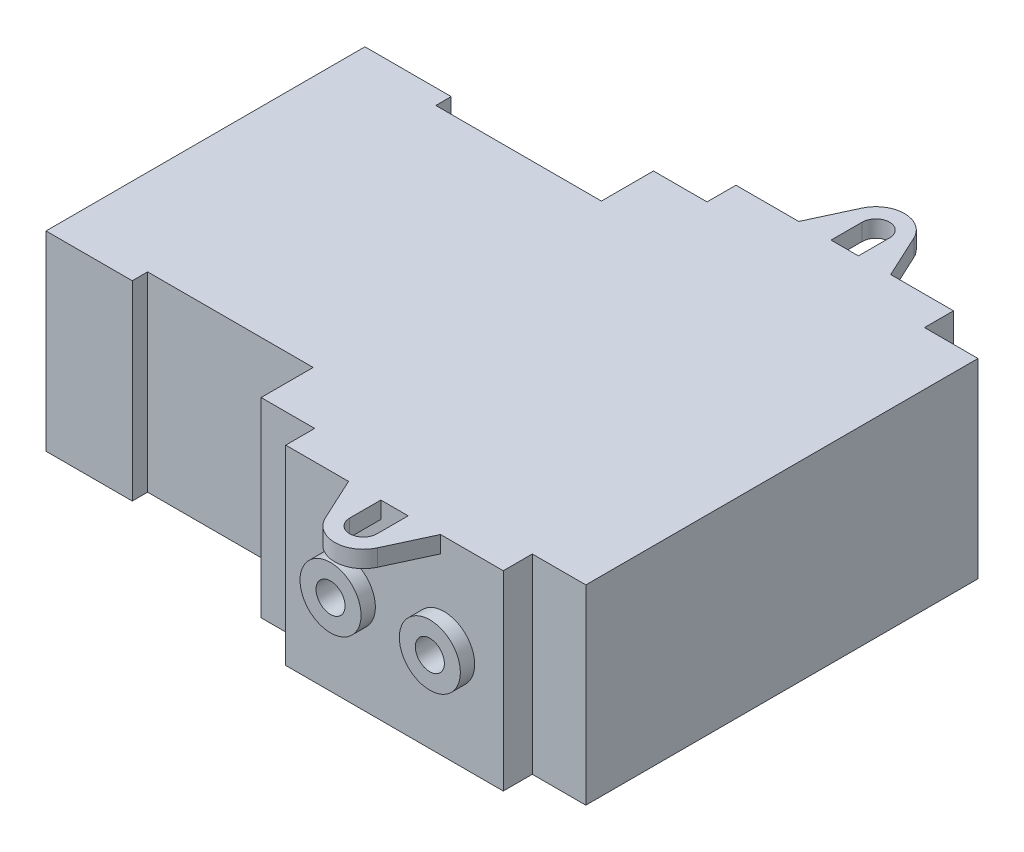
SolidWorks part; units mm, degrees
ref_plane "Front Plane" through (0, 0, 0) normal (0, 0, 1) x (1, 0, 0)
ref_plane "Top Plane" through (0, 0, 0) normal (0, 1, 0) x (1, 0, 0)
ref_plane "Right Plane" through (0, 0, 0) normal (1, 0, 0) x (0, 0, -1)
sketch "Sketch1" plane through (0, 0, 0) normal (0, 1, 0) x (1, 0, 0)
  line L0 (-34.798, 19.2532) -> (-24.384, 19.2532)
  line L1 (2.0701, 27.178) -> (28.3337, 27.178)
  line L2 (-34.798, 19.2532) -> (-34.798, -19.2532)
  line L3 (15.2019, 36.5172) -> (15.2019, 6.6677) construction
  line L4 (34.798, 23.6728) -> (34.798, -23.6728)
  line L5 (-34.2309, 27.0281) -> (35.0763, -27.6957) construction
  line L6 (-34.798, -27.178) -> (34.798, 27.178) construction
  line L7 (-24.384, 19.2532) -> (-24.384, 17.399)
  line L8 (-24.384, 17.399) -> (-4.3942, 17.399)
  line L9 (-4.3942, 17.399) -> (-4.3942, 23.6847)
  line L10 (0, 0) -> (-64.5877, 0) construction
  line L11 (0, 0) -> (50.5641, 0) construction
  line L12 (2.0701, 27.178) -> (2.0701, 23.6847)
  line L13 (2.0701, 23.6847) -> (-4.3942, 23.6847)
  line L14 (28.3337, 27.178) -> (28.3337, 23.6728)
  line L15 (28.3337, 23.6728) -> (34.798, 23.6728)
  line L16 (28.3337, -23.6728) -> (34.798, -23.6728)
  line L17 (28.3337, -27.178) -> (28.3337, -23.6728)
  line L18 (2.0701, -27.178) -> (28.3337, -27.178)
  line L19 (2.0701, -27.178) -> (2.0701, -23.6847)
  line L20 (2.0701, -23.6847) -> (-4.3942, -23.6847)
  line L21 (-4.3942, -17.399) -> (-4.3942, -23.6847)
  line L22 (-24.384, -17.399) -> (-4.3942, -17.399)
  line L23 (-34.798, -19.2532) -> (-24.384, -19.2532)
  line L24 (-24.384, -17.399) -> (-24.384, -19.2532)
  point P0 (0, 0)
  point P23 (34.798, 0)
  point P33 (-34.798, 0)
  dimension "D1" = 69.596
  dimension "D2" = 27.178
  dimension "D3" = 10.414
  dimension "D4" = 39.1922
  dimension "D5" = 9.779
  dimension "D6" = 1.8542
  dimension "D7" = 13.1318
  dimension "D8" = 13.1318
  dimension "D9" = 19.5961
  dimension "D10" = 3.5052
extrude "Boss-Extrude1" add sketch "Sketch1" along normal blind 23.0378
sketch "Sketch2" plane through (0, 0, 27.178) normal (0, 0, 1) x (1, 0, 0)
  line L0 (15.2019, 23.0378) -> (15.2019, -4.46) construction
  line L1 (2.0701, 23.0378) -> (28.3337, 23.0378) construction
  circle A0 centre (21.1963, 11.5189) radius 3.683
  circle A1 centre (9.2075, 11.5189) radius 3.683
  dimension "D1" = 7.366
  dimension "D2" = 7.366
  dimension "D3" = 5.9944
  dimension "D4" = 5.9944
  dimension "D5" = 11.5189
extrude "Boss-Extrude2" add sketch "Sketch2" along normal blind 1.7272
mirror "Mirror1" about plane through (0, 0, 0) normal (0, 0, 1) of "Boss-Extrude2"
sketch "Sketch3" plane through (0, 0, 28.9052) normal (0, 0, 1) x (1, 0, 0)
  circle A0 centre (21.1963, 11.5189) radius 1.7526
  circle A1 centre (9.2075, 11.5189) radius 1.7526
  dimension "D1" = 3.5052
  dimension "D2" = 3.5052
extrude "Cut-Extrude1" cut sketch "Sketch3" against normal through all
sketch "Sketch4" plane through (0, 23.0378, 0) normal (0, 1, 0) x (1, 0, 0)
  line L0 (15.2019, -33.1206) -> (15.2019, 43.2988) construction
  line L1 (9.652, -27.178) -> (12.0678, -32.3899)
  line L2 (2.0701, -27.178) -> (28.3337, -27.178) construction
  line L3 (20.7518, -27.178) -> (18.336, -32.3899)
  line L4 (15.2019, -39.1514) -> (14.9858, -39.6177)
  line L5 (40.7981, 0) -> (-39.0177, 0) construction
  line L6 (28.3337, -27.178) -> (28.3337, -23.6728) construction
  line L7 (15.2019, -39.1514) -> (15.504, -39.8033)
  line L8 (13.5509, -30.9372) -> (13.5509, -27.178)
  line L9 (16.8529, -30.9372) -> (16.8529, -27.178)
  line L10 (16.8529, -27.178) -> (20.7518, -27.178)
  line L11 (13.5509, -27.178) -> (9.652, -27.178)
  line L12 (16.8529, 27.178) -> (20.7518, 27.178)
  line L13 (13.5509, 27.178) -> (9.652, 27.178)
  line L14 (13.5509, 30.9372) -> (13.5509, 27.178)
  line L15 (16.8529, 30.9372) -> (16.8529, 27.178)
  line L16 (20.7518, 27.178) -> (18.336, 32.3899)
  line L17 (9.652, 27.178) -> (12.0678, 32.3899)
  arc A0 (12.0678, -32.3899) -> (18.336, -32.3899) centre (15.2019, -30.9372) ccw
  arc A1 (13.5509, -30.9372) -> (16.8529, -30.9372) centre (15.2019, -30.9372) ccw
  arc A2 (13.5509, 30.9372) -> (16.8529, 30.9372) centre (15.2019, 30.9372) cw
  arc A3 (12.0678, 32.3899) -> (18.336, 32.3899) centre (15.2019, 30.9372) cw
  line M8 (2.0701, -27.178) -> (28.3337, -27.178)
  line M14 (28.3337, 27.178) -> (2.0701, 27.178)
  dimension "D1" = 6.9088
  dimension "D2" = 3.302
  dimension "D3" = 30.9372
  dimension "D4" = 13.1318
  dimension "D5" = 5.5499
  dimension "D6" = 5.5499
extrude "Boss-Extrude3" add sketch "Sketch4" against normal blind 2.032 contours A1 L8 L1 A0 L3 L9 M8 | A3 L17 L14 A2 L15 L16 M14
